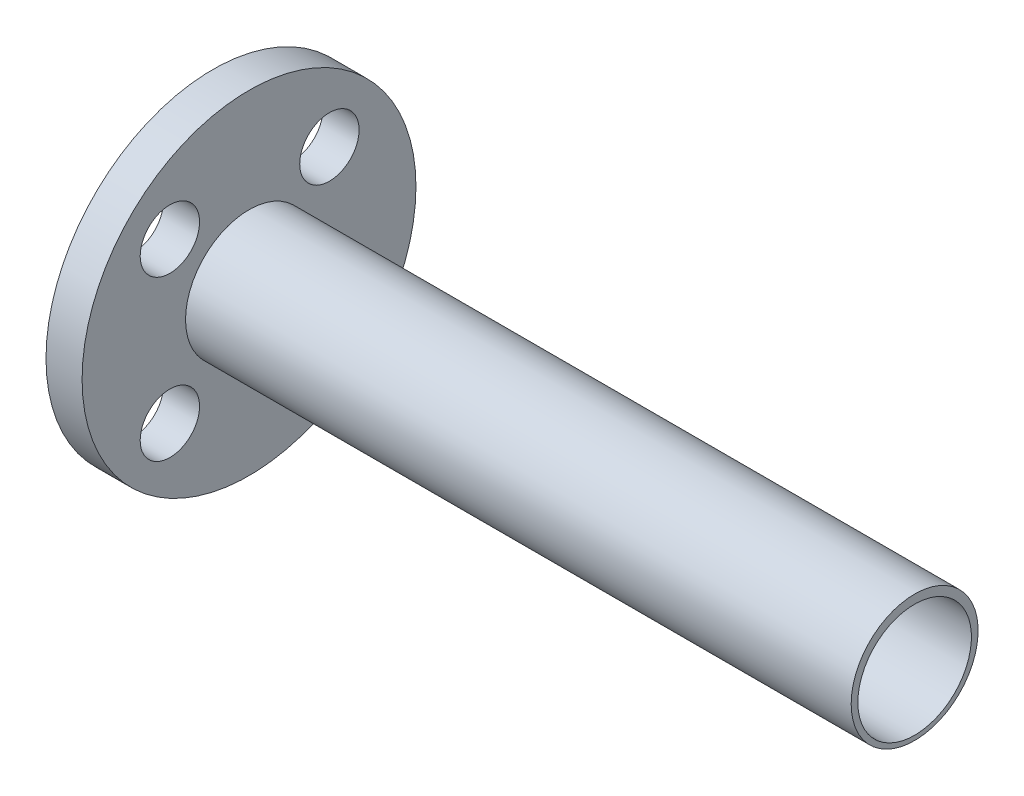
SolidWorks part; units mm, degrees
ref_plane "Front Plane" through (0, 0, 0) normal (0, 0, 1) x (1, 0, 0)
ref_plane "Top Plane" through (0, 0, 0) normal (0, 1, 0) x (1, 0, 0)
ref_plane "Right Plane" through (0, 0, 0) normal (1, 0, 0) x (0, 0, -1)
sketch "Sketch1" plane through (0, 0, 0) normal (0, 0, 1) x (1, 0, 0)
  line L1 (53.975, 0.5551) -> (53.975, 11.176)
  line L2 (52.451, 45.1854) -> (62.101, 45.1854)
  line L4 (53.975, 0.5551) -> (240.0615, 0.5551)
  line L5 (62.101, 45.1854) -> (62.101, 17.526)
  line L6 (62.101, 17.526) -> (240.0615, 17.526)
  line L7 (240.0615, 17.526) -> (240.0615, 0.5551)
  line L18 (52.451, 17.526) -> (52.451, 45.1854)
  line L19 (53.975, 17.526) -> (52.451, 17.526)
  line L20 (53.975, 11.176) -> (53.975, 17.526)
revolve "Revolve1" add sketch "Sketch1" angle 360 about L4
sketch "Sketch3" plane through (53.975, 0, 0) normal (-1, 0, 0) x (0, 0, 1)
  circle A1 centre (0, 0) radius 15.18
extrude "Cut-Extrude1" cut sketch "Sketch3" against normal through all contours A1
sketch "Sketch5" plane through (52.451, 0, 0) normal (-1, 0, 0) x (0, 0, 1)
  circle A0 centre (-21.4944, 21.3142) radius 7.9375
  circle A1 centre (-21.4944, -21.342) radius 7.9375
  circle A2 centre (21.1618, 21.3142) radius 7.9375
  circle A3 centre (21.1618, -21.342) radius 7.9375
  point P0 (0, 0)
extrude "Cut-Extrude2" cut sketch "Sketch5" against normal blind 10
